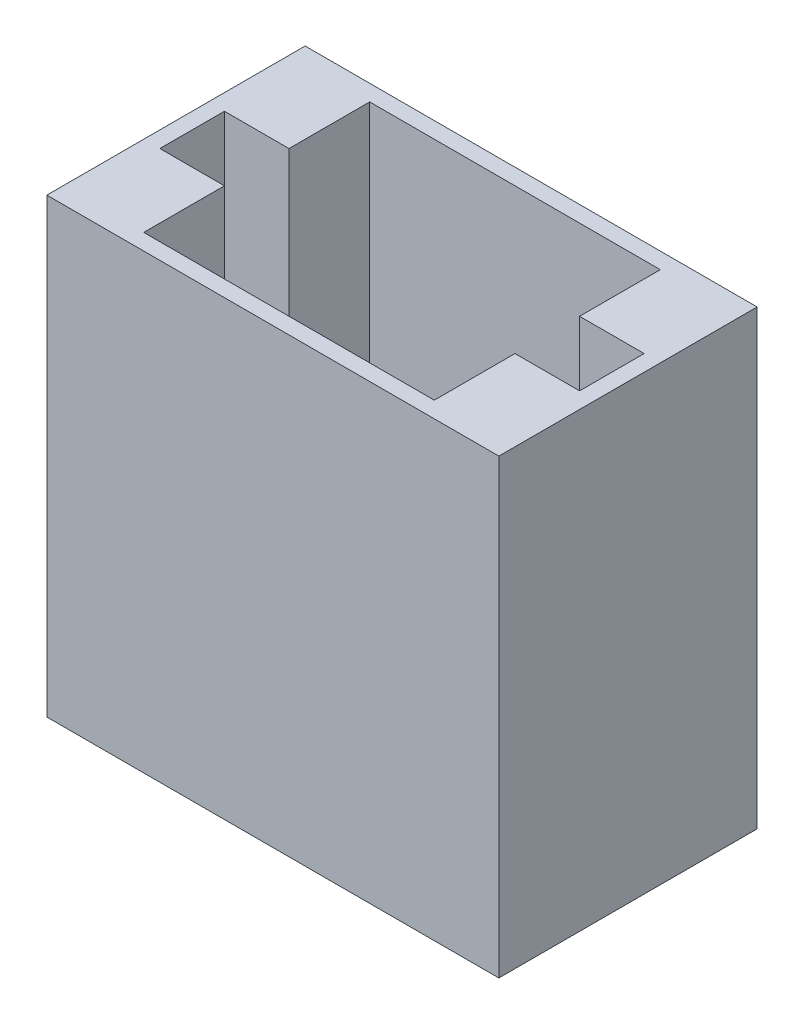
SolidWorks part; units mm, degrees
ref_plane "Front Plane" through (0, 0, 0) normal (0, 0, 1) x (1, 0, 0)
ref_plane "Top Plane" through (0, 0, 0) normal (0, 1, 0) x (1, 0, 0)
ref_plane "Right Plane" through (0, 0, 0) normal (1, 0, 0) x (0, 0, -1)
sketch "Sketch3" plane through (0, 0, 0) normal (0, 1, 0) x (1, 0, 0)
  line L1 (-35, -20) -> (35, -20)
  line L2 (-35, -20) -> (-35, 20)
  line L3 (-35, 20) -> (35, 20)
  line L4 (35, -20) -> (35, 20)
  line L5 (-35, -20) -> (35, 20) construction
  line L6 (-35, 20) -> (35, -20) construction
  point P0 (0, 0)
  dimension "D1" = 40
  dimension "D2" = 70
extrude "Boss-Extrude2" add sketch "Sketch3" along normal blind 70
sketch "Sketch4" plane through (0, 70, 0) normal (0, 1, 0) x (1, 0, 0)
  line L1 (-32.5, 17.5) -> (32.5, 17.5)
  line L2 (-32.5, 17.5) -> (-32.5, -17.5)
  line L3 (-32.5, -17.5) -> (32.5, -17.5)
  line L4 (32.5, 17.5) -> (32.5, -17.5)
  line L5 (-32.5, 17.5) -> (32.5, -17.5) construction
  line L6 (-32.5, -17.5) -> (32.5, 17.5) construction
  point P0 (0, 0)
  dimension "D1" = 65
  dimension "D2" = 35
extrude "Cut-Extrude1" cut sketch "Sketch4" against normal through all
sketch "Sketch5" plane through (-32.5, 0, 0) normal (1, 0, 0) x (0, 0, -1)
  line L0 (0, 84.6724) -> (0, -27.2944) construction
  line L1 (17.5, 0) -> (-17.5, 0) construction
  line L2 (17.5, 70) -> (-17.5, 70) construction
  line L3 (0, 70) -> (-17.5, 70)
  line L4 (-17.5, 70) -> (-17.5, 0)
  line L5 (-17.5, 0) -> (-17.5, 70) construction
  line L6 (-17.5, 0) -> (17.5, 0)
  line L7 (17.5, 0) -> (17.5, 70)
  line L8 (17.5, 70) -> (-17.5, 70)
  line L9 (-5, 70) -> (-5, 0)
  line L10 (5, 70) -> (5, 0)
  line M3 (17.5, 70) -> (-17.5, 70)
  line M4 (-17.5, 70) -> (-17.5, 0)
  line M5 (-17.5, 0) -> (17.5, 0)
  line M6 (17.5, 0) -> (17.5, 70)
  dimension "D1" = 5
extrude "Boss-Extrude3" add sketch "Sketch5" along normal blind 10 contours L9 L8 M4 M5 | L10 M3 M5 M6
mirror "Mirror1" about plane through (0, 0, 0) normal (1, 0, 0) of "Boss-Extrude3"
